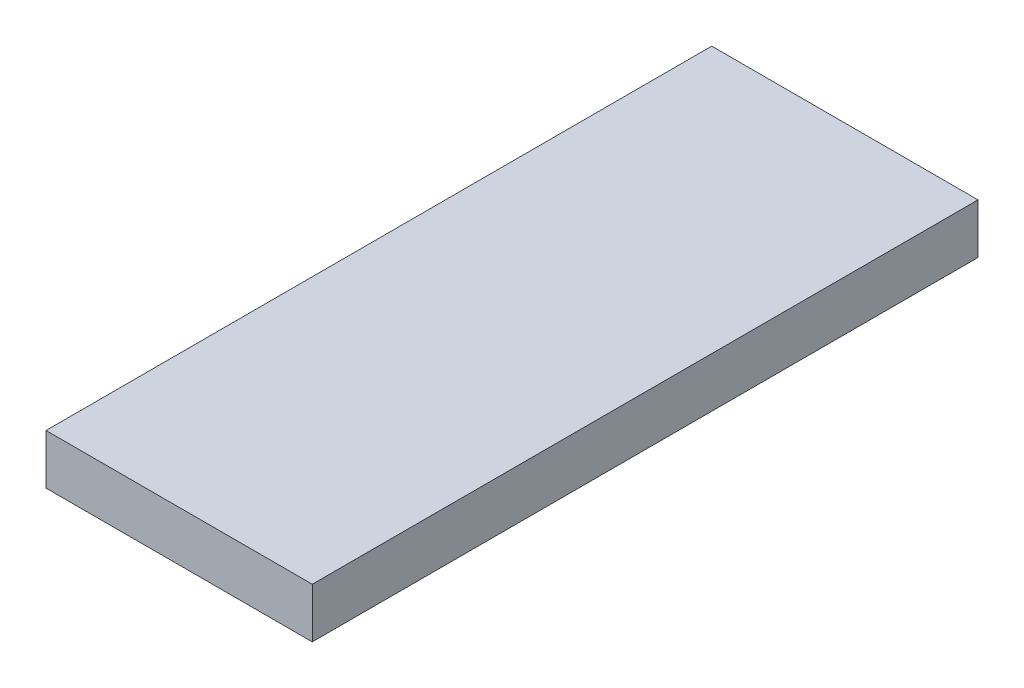
SolidWorks part; units mm, degrees
material "橡胶"
ref_plane "前视基准面" through (0, 0, 0) normal (0, 0, 1) x (1, 0, 0)
ref_plane "上视基准面" through (0, 0, 0) normal (0, 1, 0) x (1, 0, 0)
ref_plane "右视基准面" through (0, 0, 0) normal (1, 0, 0) x (0, 0, -1)
sketch "草图1" plane through (0, 0, 0) normal (0, 1, 0) x (1, 0, 0)
  line L1 (-8, 20) -> (8, 20)
  line L2 (-8, 20) -> (-8, -20)
  line L3 (-8, -20) -> (8, -20)
  line L4 (8, 20) -> (8, -20)
  line L5 (-8, 20) -> (8, -20) construction
  line L6 (-8, -20) -> (8, 20) construction
  point P0 (0, 0)
  dimension "D1" = 16
  dimension "D2" = 40
extrude "凸台-拉伸1" add sketch "草图1" along normal blind 3
sketch "草图2" plane through (0, 3, 0) normal (0, 1, 0) x (1, 0, 0)
  circle A0 centre (0, 0) radius 5.8096
